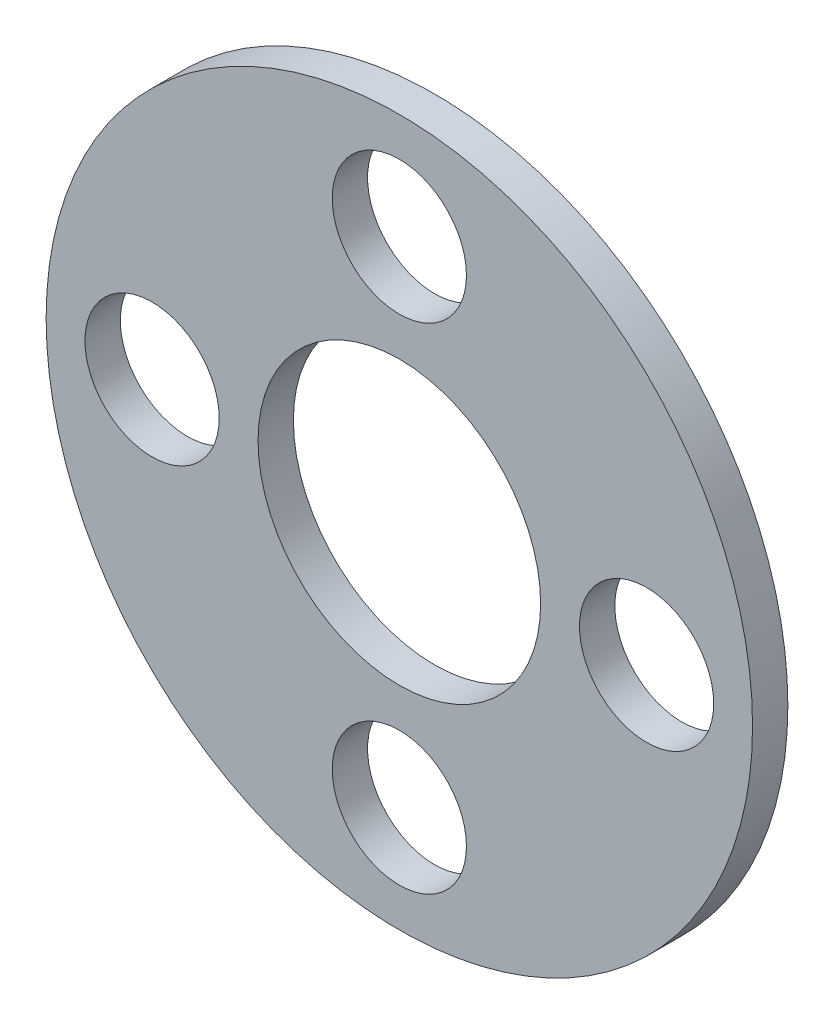
SolidWorks part; units mm, degrees
ref_plane "Front" through (0, 0, 0) normal (0, 0, 1) x (1, 0, 0)
ref_plane "Top" through (0, 0, 0) normal (0, 1, 0) x (1, 0, 0)
ref_plane "Right" through (0, 0, 0) normal (1, 0, 0) x (0, 0, -1)
sketch "Esquisse1" plane through (0, 0, 0) normal (0, 0, 1) x (1, 0, 0)
  circle A0 centre (0, 0) radius 10
  circle A1 centre (0, 0) radius 4
  dimension "D1" = 20
  dimension "D2" = 8
extrude "Boss.-Extru.1" add sketch "Esquisse1" along normal blind 1
sketch "Esquisse2" plane through (0, 0, 1) normal (0, 0, 1) x (1, 0, 0)
  line L0 (0, 0) -> (7, 0) construction
  circle A0 centre (7, 0) radius 1.9
  circle A1 centre (0, -7) radius 1.9
  circle A2 centre (-7, 0) radius 1.9
  circle A3 centre (0, 7) radius 1.9
  point P13 (0, 0)
  dimension "D1" = 3.8
  dimension "D2" = 7
  dimension "D3" = 4
extrude "Enlèv. mat.-Extru.1" cut sketch "Esquisse2" against normal through all both and the other way through all
